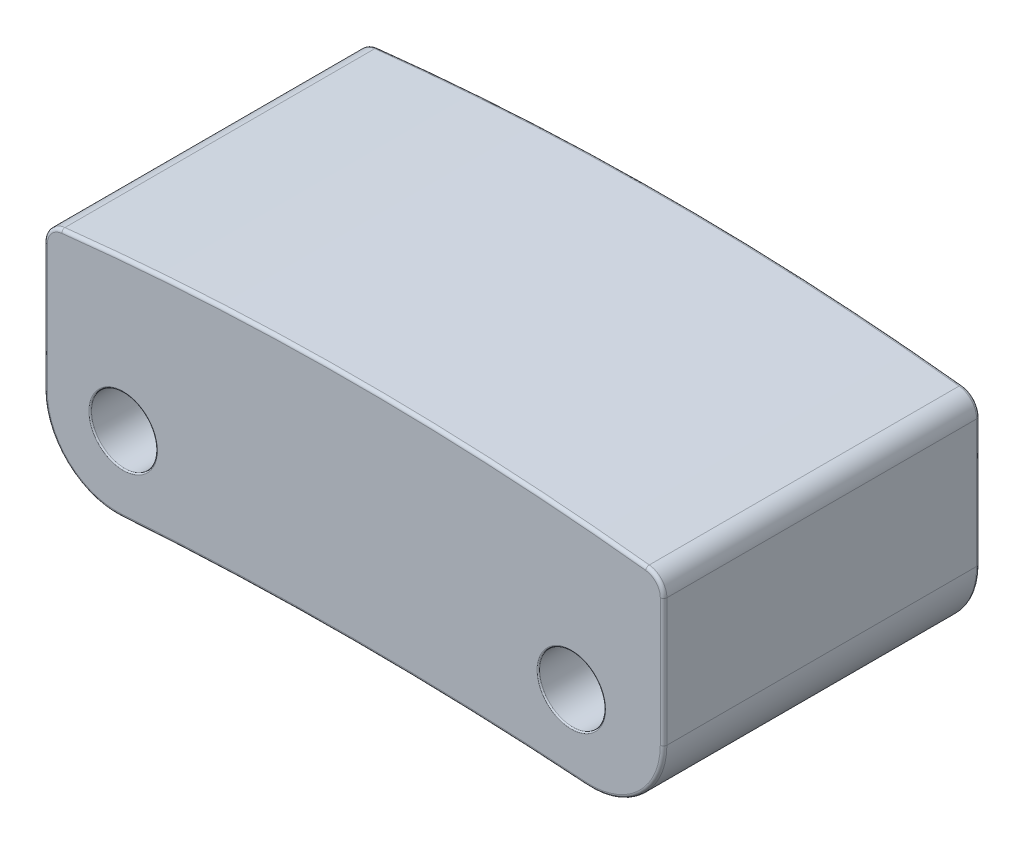
SolidWorks part; units mm, degrees
ref_plane "Front Plane" through (0, 0, 0) normal (0, 0, 1) x (1, 0, 0)
ref_plane "Top Plane" through (0, 0, 0) normal (0, 1, 0) x (1, 0, 0)
ref_plane "Right Plane" through (0, 0, 0) normal (1, 0, 0) x (0, 0, -1)
sketch "Sketch1" plane through (0, 0, 0) normal (0, 0, 1) x (1, 0, 0)
  line L0 (55, 0) -> (-55, 0) construction
  line L1 (-4.7, 1.85) -> (4.7, 1.85)
  line L2 (-4.7, 1.85) -> (-4.7, -1.85)
  line L3 (-4.7, -1.85) -> (4.7, -1.85)
  line L4 (4.7, 1.85) -> (4.7, -1.85)
  line L5 (0, -55) -> (0, 55) construction
  dimension "D1" = 9.4
  dimension "D2" = 3.7
  dimension "D3" = 1.85
  dimension "D4" = 4.7
extrude "Boss-Extrude1" add sketch "Sketch1" along normal mid plane 4.8
sketch "Sketch2" plane through (0, 0, 2.4) normal (0, 0, 1) x (1, 0, 0)
  line L0 (-4.7, 1.85) -> (-4.7, -1.85) construction
  line L1 (4.7, -1.85) -> (4.7, 1.85) construction
  line L2 (-4.7, -1.85) -> (4.7, -1.85) construction
  line L3 (4.7, 1.85) -> (-4.7, 1.85) construction
  line L4 (-4.7, 1.55) -> (-7.1207, 4.0114)
  line L5 (-7.1207, 4.0114) -> (5.5359, 3.8867)
  line L6 (5.5359, 3.8867) -> (4.7, 1.55)
  line L7 (4.7, -1.85) -> (0.3506, -3.782)
  line L8 (-4.7, -1.85) -> (0.3506, -3.782)
  arc A0 (-4.7, 1.55) -> (4.7, 1.55) centre (0, -38.1729) cw
  arc A1 (-4.7, -1.85) -> (4.7, -1.85) centre (0, -51.6286) cw
  dimension "D4" = 40
  dimension "D5" = 50
  dimension "D1" = 0
  dimension "D2" = 0.3
  dimension "D3" = 0.3
extrude "Cut-Extrude1" cut sketch "Sketch2" against normal blind 4.8
fillet "Fillet1" radius 1.1 2 edges at (4.7, -1.85, 0) (-4.7, -1.85, 0)
fillet "Fillet2" radius 0.3 2 edges at (4.7, 1.55, 0) (-4.7, 1.55, 0)
fillet "Fillet3" radius 0.05 16 edges at (-4.6236, 1.4825, -2.4) (-4.7, 0.3135, -2.4) (-4.3499, -1.4603, -2.4) (0, -1.6286, -2.4) (4.3499, -1.4603, -2.4) (4.7, 0.3135, -2.4) (4.6236, 1.4825, -2.4) (0, 1.8271, -2.4) (4.3499, -1.4603, 2.4) (0, -1.6286, 2.4) (-4.3499, -1.4603, 2.4) (-4.7, 0.3135, 2.4) (-4.6236, 1.4825, 2.4) (0, 1.8271, 2.4) (4.6236, 1.4825, 2.4) (4.7, 0.3135, 2.4)
sketch "Sketch3" plane through (0, 0, 2.4) normal (0, 0, 1) x (1, 0, 0)
  line L0 (2.64, 0) -> (-2.64, 0) construction
  line L1 (0, -1.9705) -> (0, 1.9705) construction
  circle A0 centre (3.3, -0.6) radius 0.5
  circle A1 centre (-3.5, -0.6) radius 0.5
  dimension "D1" = 1
  dimension "D3" = 0.6
  dimension "D4" = 1
  dimension "D5" = 3.5
  dimension "D6" = 3.3
  dimension "D2" = 0.6
extrude "Cut-Extrude2" cut sketch "Sketch3" against normal blind 4.8 from offset 1
fillet "Fillet4" radius 0.02 2 edges at (3.8, -0.6, 2.4) (-3, -0.6, 2.4)
sketch "Sketch4" plane through (0, 0, 0) normal (0, 1, 0) x (1, 0, 0)
  line L1 (-3.526, -2.4) -> (3.526, -2.4) construction
  line L2 (-4.7, 2.35) -> (-4.7, -2.35) construction
  circle A0 centre (-0.05, -0.9) radius 0.4
  dimension "D1" = 0.8
  dimension "D2" = 1.5
  dimension "D3" = 4.65
extrude "Cut-Extrude3" cut sketch "Sketch4" along normal offset from surface (8.7714 mm away) 0.4 from offset 10 offset against normal yes
fillet "Fillet5" radius 0.05 1 edges at (-0.142, -1.6288, 1.2893)
